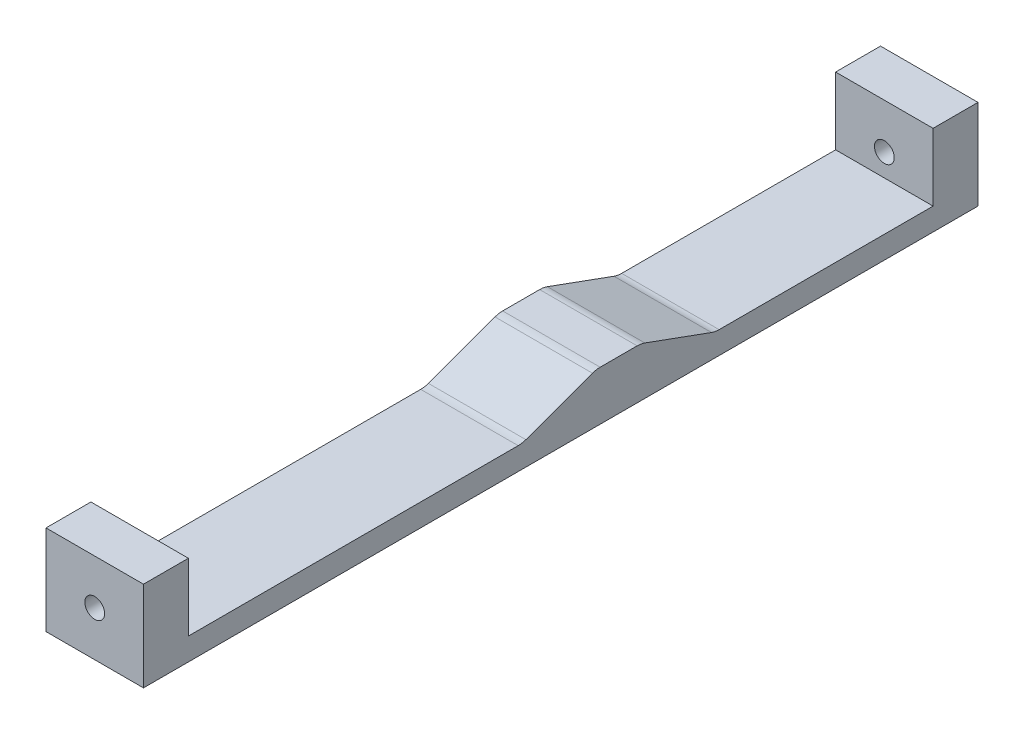
SolidWorks part; units mm, degrees
ref_plane "Front Plane" through (0, 0, 0) normal (0, 0, 1) x (1, 0, 0)
ref_plane "Top Plane" through (0, 0, 0) normal (0, 1, 0) x (1, 0, 0)
ref_plane "Right Plane" through (0, 0, 0) normal (1, 0, 0) x (0, 0, -1)
sketch "Sketch1" plane through (0, 0, 0) normal (0, 1, 0) x (1, 0, 0)
  line L1 (-6.8898, -58.9865) -> (6.8897, -58.9865)
  line L2 (-6.8898, -58.9865) -> (-6.8898, 58.9865)
  line L3 (-6.8898, 58.9865) -> (6.8897, 58.9865)
  line L4 (6.8897, -58.9865) -> (6.8897, 58.9865)
  line L5 (-6.8898, -58.9865) -> (6.8897, 58.9865) construction
  line L6 (-6.8898, 58.9865) -> (6.8897, -58.9865) construction
  point P0 (0, 0)
  point P6 (0, 0)
  dimension "D1" = 13.7795
  dimension "D2" = 117.973
extrude "Boss-Extrude1" add sketch "Sketch1" along normal blind 3.175
sketch "Sketch4" plane through (0, 0, 58.9865) normal (0, 0, 1) x (1, 0, 0)
  circle A0 centre (0, 6.35) radius 1.4
  dimension "D1" = 2.8
  dimension "D2" = 6.35
sketch "Sketch5" plane through (0, 0, 58.9865) normal (0, 0, 1) x (1, 0, 0)
  line L1 (-6.8898, 3.175) -> (6.8897, 3.175)
  line L2 (-6.8898, 3.175) -> (-6.8898, 12.7)
  line L3 (-6.8898, 12.7) -> (6.8897, 12.7)
  line L4 (6.8897, 3.175) -> (6.8897, 12.7)
  dimension "D1" = 9.525
extrude "Boss-Extrude2" add sketch "Sketch5" against normal blind 6.35
mirror "Mirror1" about plane through (0, 0, 0) normal (0, 0, 1) of "Boss-Extrude2"
extrude "Cut-Extrude1" cut sketch "Sketch4" against normal through all
sketch "Sketch6" plane through (-6.8898, 0, 0) normal (-1, 0, 0) x (0, 0, 1)
  line L0 (-11.3615, 6.985) -> (-5.0115, 6.985)
  line L1 (-58.9865, 12.7) -> (-58.9865, 0) construction
  line L2 (-11.3615, 6.985) -> (-21.8294, 3.175)
  line L3 (-52.6365, 3.175) -> (52.6365, 3.175) construction
  line L4 (-21.8294, 3.175) -> (5.4564, 3.175)
  line L5 (5.4564, 3.175) -> (-5.0115, 6.985)
  point P2 (-8.1865, 6.985)
  dimension "D1" = 50.8
  dimension "D2" = 6.35
  dimension "D3" = 20
  dimension "D4" = 20
  dimension "D5" = 3.81
extrude "Boss-Extrude3" add sketch "Sketch6" against normal up to surface (13.7795 mm away) up to face at (6.8897, 7.1437, 0)
fillet "Fillet1" radius 3.175 4 edges at (0, 3.175, 5.4564) (0, 6.985, -5.0115) (0, 3.175, -21.8294) (0, 6.985, -11.3615)
equation "\"tighttol\" = 0.005in"
equation "\"normtol\" = 0.01in"
equation "\"loosetol\" = 0.02in"
equation "\"Fry height\"= 0.5in"
equation "\"Fry spacing\"= 0.5625in"
equation "\"Potato width\"= \"Fry spacing\" * 4"
equation "\"Potato length\"= 80mm"
equation "\"D1@Sketch1\"=\"Fry spacing\" - \"loosetol\""
equation "\"D2@Sketch1\"=\"Potato length\"+1.5-\"tighttol\""
equation "\"D1@Sketch4\"=2.8mm"
